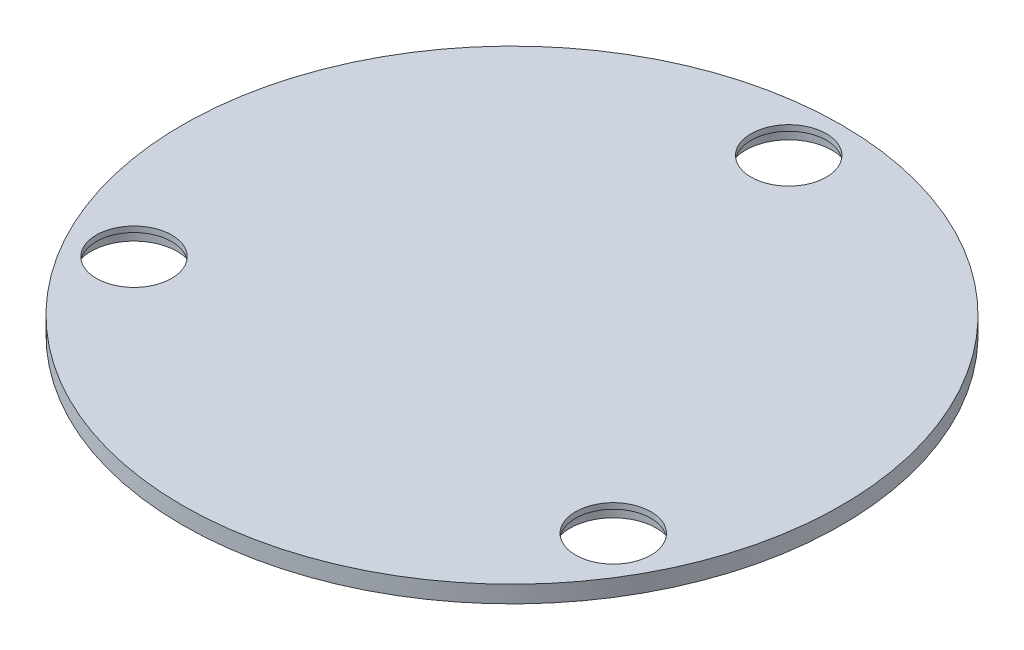
SolidWorks part; units mm, degrees
ref_plane "Front Plane" through (0, 0, 0) normal (0, 0, 1) x (1, 0, 0)
ref_plane "Top Plane" through (0, 0, 0) normal (0, 1, 0) x (1, 0, 0)
ref_plane "Right Plane" through (0, 0, 0) normal (1, 0, 0) x (0, 0, -1)
sketch "Sketch1" plane through (0, 0, 0) normal (0, 1, 0) x (1, 0, 0)
  circle A0 centre (0, 0) radius 58
  circle A1 centre (0, 48.6995) radius 6.625
  circle A2 centre (42.175, -24.3497) radius 6.625
  circle A3 centre (-42.175, -24.3497) radius 6.625
  point P5 (0, 0)
  point P6 (0, 0)
  point P7 (0, 0)
  point P12 (0, 0)
  dimension "D1" = 116
  dimension "D2" = 13.25
  dimension "D4" = 84.35
  dimension "D3" = 3
extrude "Boss-Extrude1" add sketch "Sketch1" along normal blind 3
sketch "Sketch2" plane through (0, 0, 0) normal (0, -1, 0) x (1, 0, 0)
  circle A21 centre (42.175, 24.3497) radius 7.6
  circle A22 centre (-42.175, 24.3497) radius 7.6
  circle A23 centre (0, -48.6995) radius 7.6
  dimension "D1" = 15.2
extrude "Cut-Extrude1" cut sketch "Sketch2" against normal blind 2
